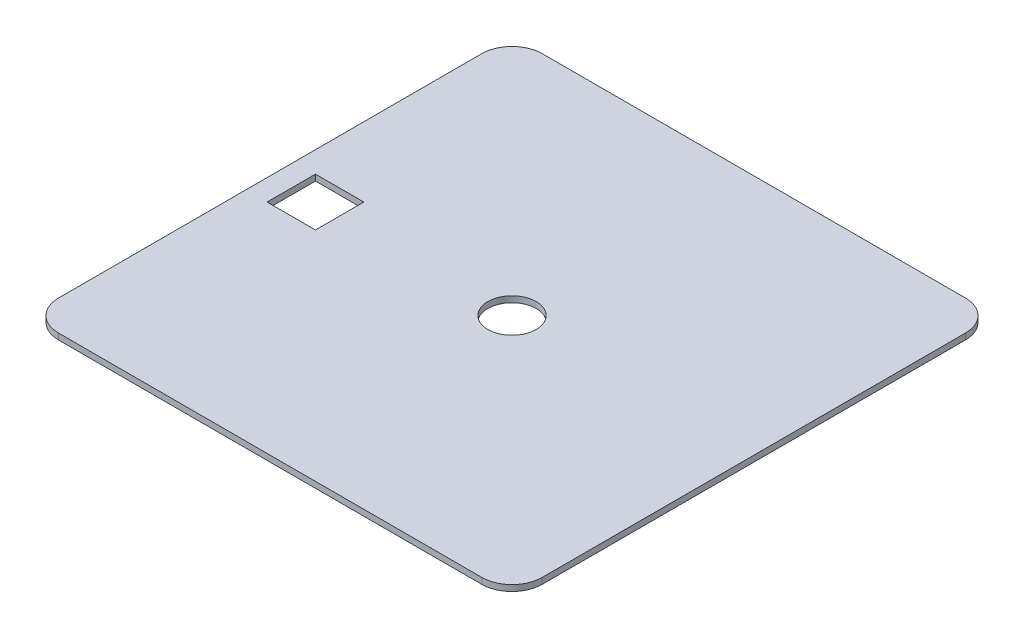
SolidWorks part; units mm, degrees
ref_plane "Face" through (0, 0, 0) normal (0, 0, 1) x (1, 0, 0)
ref_plane "Dessus" through (0, 0, 0) normal (0, 1, 0) x (1, 0, 0)
ref_plane "Droite" through (0, 0, 0) normal (1, 0, 0) x (0, 0, -1)
sketch "Esquisse1" plane through (0, 0, 0) normal (0, 1, 0) x (1, 0, 0)
  line L1 (0, 0) -> (80, 0)
  line L2 (0, 0) -> (0, 80)
  line L3 (0, 80) -> (80, 80)
  line L4 (80, 0) -> (80, 80)
  dimension "D1" = 80
  dimension "D2" = 80
extrude "Extrusion1" add sketch "Esquisse1" along normal blind 1
fillet "Congé1" radius 5 4 edges at (80, 0.5, -80) (80, 0.5, 0) (0, 0.5, 0) (0, 0.5, -80)
sketch "Esquisse3" plane through (0, 1, 0) normal (0, 1, 0) x (1, 0, 0)
  line L1 (0, 75) -> (0, 5) construction
  line L2 (5, 0) -> (75, 0) construction
  circle A0 centre (40, 40) radius 4
  dimension "D1" = 8
  dimension "D2" = 40
  dimension "D3" = 40
extrude "Enlèv. mat.-Extru.1" cut sketch "Esquisse3" against normal through all
sketch "Esquisse4" plane through (0, 1, 0) normal (0, 1, 0) x (1, 0, 0)
  line L0 (75, 80) -> (5, 80) construction
  line L1 (3.5, 44) -> (11.5, 44)
  line L2 (3.5, 44) -> (3.5, 36)
  line L3 (3.5, 36) -> (11.5, 36)
  line L4 (11.5, 44) -> (11.5, 36)
  line L5 (0, 75) -> (0, 5) construction
  dimension "D1" = 8
  dimension "D2" = 8
  dimension "D3" = 36
  dimension "D4" = 3.5
extrude "Enlèv. mat.-Extru.2" cut sketch "Esquisse4" against normal through all
